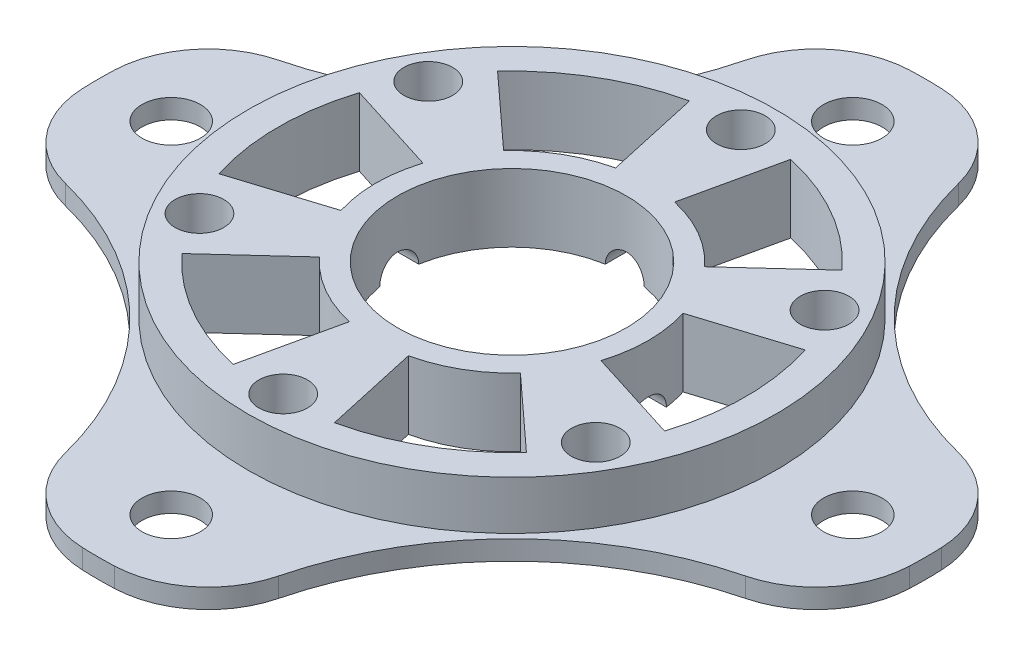
SolidWorks part; units mm, degrees
ref_plane "Front Plane" through (0, 0, 0) normal (0, 0, 1) x (1, 0, 0)
ref_plane "Top Plane" through (0, 0, 0) normal (0, 1, 0) x (1, 0, 0)
ref_plane "Right Plane" through (0, 0, 0) normal (1, 0, 0) x (0, 0, -1)
sketch "Sketch1" plane through (0, 0, 0) normal (0, 1, 0) x (1, 0, 0)
  circle A0 centre (0, 0) radius 27.1
  dimension "D1" = 54.2
extrude "Boss-Extrude1" add sketch "Sketch1" against normal blind 5
sketch "Sketch2" plane through (0, -5, 0) normal (0, -1, 0) x (1, 0, 0)
  circle A0 centre (0, 0) radius 42.5
  dimension "D1" = 85
extrude "Boss-Extrude2" add sketch "Sketch2" along normal blind 2
sketch "Sketch3" plane through (0, -5, 0) normal (0, 1, 0) x (1, 0, 0)
  circle A0 centre (0, 35) radius 3
  circle A1 centre (35, 0) radius 3
  circle A2 centre (0, -35) radius 3
  circle A3 centre (-35, 0) radius 3
  circle A4 centre (0, 0) radius 42.5 construction
  arc A5 (-10, 41.3068) -> (-41.3068, 10) centre (-42.9586, 42.9586) cw
  arc A6 (41.3068, 10) -> (10, 41.3068) centre (42.9586, 42.9586) cw
  arc A7 (10, -41.3068) -> (41.3068, -10) centre (42.9586, -42.9586) cw
  arc A8 (-41.3068, -10) -> (-10, -41.3068) centre (-42.9586, -42.9586) cw
  circle A10 centre (0, 0) radius 42.5
  circle A11 centre (0, 0) radius 42.5
  point P12 (0, 0)
  point P27 (0, 0)
  circle M3 centre (0, 0) radius 42.5
  dimension "D1" = 6
  dimension "D6" = 33
  dimension "D2" = 35
  dimension "D3" = 4
  dimension "D4" = 10
  dimension "D5" = 10
  dimension "D8" = 0
  dimension "D7" = 4
extrude "Cut-Extrude1" cut sketch "Sketch3" against normal blind 2 contours A5 M3 | A0 | A6 M3 | A1 | A2 | A7 M3 | A8 M3 | A3
sketch "Sketch4" plane through (0, 0, 0) normal (0, 1, 0) x (1, 0, 0)
  circle A0 centre (0, 0) radius 11.75
  circle A1 centre (0, 23.5) radius 2.5
  circle A2 centre (20.3516, 11.75) radius 2.5
  circle A3 centre (20.3516, -11.75) radius 2.5
  circle A4 centre (0, -23.5) radius 2.5
  circle A5 centre (-20.3516, -11.75) radius 2.5
  circle A6 centre (-20.3516, 11.75) radius 2.5
  point P18 (0, 0)
  dimension "D1" = 23.5
  dimension "D2" = 5
  dimension "D3" = 23.5
  dimension "D4" = 6
extrude "Cut-Extrude2" cut sketch "Sketch4" against normal through all
sketch "Sketch5" plane through (0, 0, 0) normal (0, 1, 0) x (1, 0, 0)
  line L0 (-17.6947, 16.2142) -> (-10.3219, 9.4583)
  line L1 (-5.1946, 23.4311) -> (-3.0302, 13.6681)
  line L2 (0, 23.537) -> (0, 0) construction
  line L3 (17.6947, 16.2142) -> (10.3219, 9.4583)
  line L4 (5.1946, 23.4311) -> (3.0302, 13.6681)
  line L5 (22.8892, -7.2169) -> (13.352, -4.2099)
  line L6 (22.8892, 7.2169) -> (13.352, 4.2099)
  line L7 (5.1946, -23.4311) -> (3.0302, -13.6681)
  line L8 (17.6947, -16.2142) -> (10.3219, -9.4583)
  line L9 (-17.6947, -16.2142) -> (-10.3219, -9.4583)
  line L10 (-5.1946, -23.4311) -> (-3.0302, -13.6681)
  line L11 (-22.8892, 7.2169) -> (-13.352, 4.2099)
  line L12 (-22.8892, -7.2169) -> (-13.352, -4.2099)
  arc A0 (-10.3219, 9.4583) -> (-3.0302, 13.6681) centre (0, 0) cw
  arc A1 (-17.6947, 16.2142) -> (-5.1946, 23.4311) centre (0, 0) cw
  arc A2 (5.1946, 23.4311) -> (17.6947, 16.2142) centre (0, 0) cw
  arc A3 (3.0302, 13.6681) -> (10.3219, 9.4583) centre (0, 0) cw
  arc A4 (22.8892, 7.2169) -> (22.8892, -7.2169) centre (0, 0) cw
  arc A5 (13.352, 4.2099) -> (13.352, -4.2099) centre (0, 0) cw
  arc A6 (17.6947, -16.2142) -> (5.1946, -23.4311) centre (0, 0) cw
  arc A7 (10.3219, -9.4583) -> (3.0302, -13.6681) centre (0, 0) cw
  arc A8 (-5.1946, -23.4311) -> (-17.6947, -16.2142) centre (0, 0) cw
  arc A9 (-3.0302, -13.6681) -> (-10.3219, -9.4583) centre (0, 0) cw
  arc A10 (-22.8892, -7.2169) -> (-22.8892, 7.2169) centre (0, 0) cw
  arc A11 (-13.352, -4.2099) -> (-13.352, 4.2099) centre (0, 0) cw
  point P30 (0, 0)
  dimension "D2" = 14
  dimension "D3" = 35
  dimension "D4" = 12.5
  dimension "D1" = 10
  dimension "D5" = 6
extrude "Cut-Extrude3" cut sketch "Sketch5" against normal through all
fillet "Fillet1" radius 10 8 edges at (41.3068, -6, -10) (10, -6, -41.3068) (-10, -6, -41.3068) (-41.3068, -6, -10) (-41.3068, -6, 10) (-10, -6, 41.3068) (10, -6, 41.3068) (41.3068, -6, 10)
sketch "Sketch7" plane through (0, 0, 0) normal (1, 0, 0) x (0, 0, -1)
  line L0 (-1.6425, -7) -> (1.6425, -7) construction
  circle A0 centre (0, -7) radius 2
  dimension "D1" = 4
extrude "Cut-Extrude4" cut sketch "Sketch7" against normal mid plane 30
sketch "Sketch8" plane through (0, 0, 0) normal (0, 0, 1) x (1, 0, 0)
  line L0 (-1.6425, -7) -> (1.6425, -7) construction
  circle A0 centre (0, -7) radius 2
  dimension "D1" = 4
extrude "Cut-Extrude5" cut sketch "Sketch8" against normal mid plane 50
